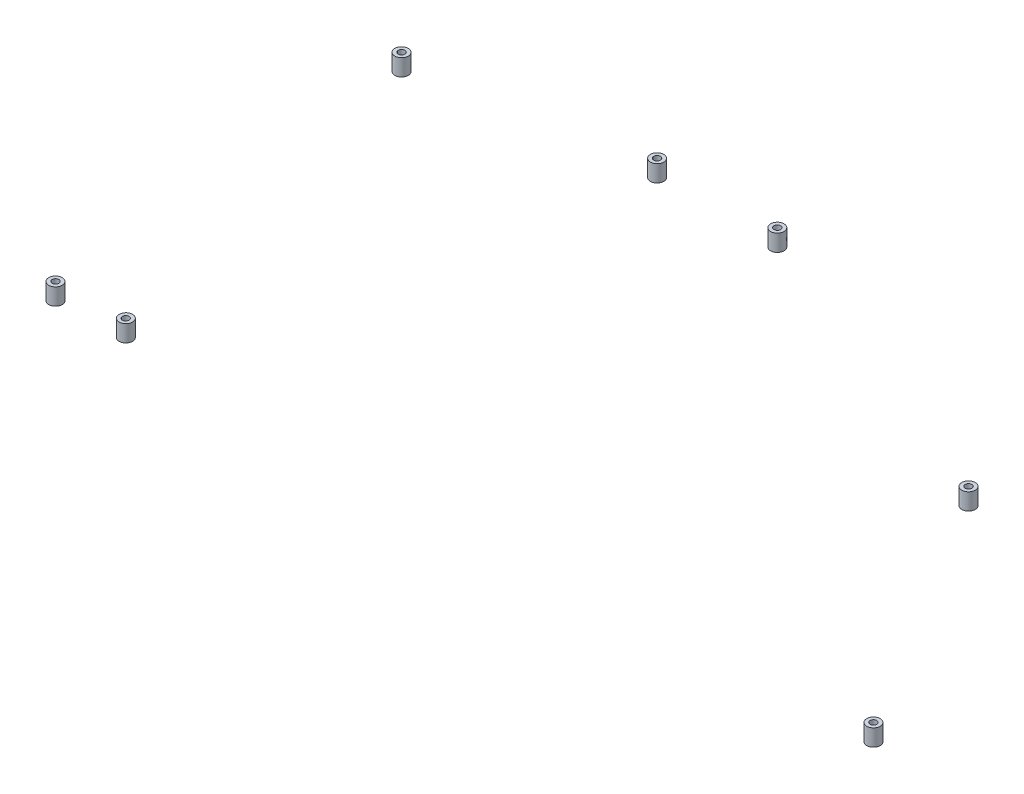
SolidWorks part; units mm, degrees
material "PP Kopolimer"
ref_plane "Płaszczyzna XY" through (0, 0, 0) normal (0, 0, 1) x (1, 0, 0)
ref_plane "Płaszczyzna XZ" through (0, 0, 0) normal (0, 1, 0) x (1, 0, 0)
ref_plane "Płaszczyzna YZ" through (0, 0, 0) normal (1, 0, 0) x (0, 0, -1)
sketch "Szkic1" plane through (0, 455.3, 0) normal (0, 1, 0) x (1, 0, 0)
  circle A0 centre (-557.5005, -428.0764) radius 4 construction
  circle A1 centre (-517.5005, -426.0794) radius 4 construction
  circle A2 centre (-85.5135, -411.9205) radius 4 construction
  circle A4 centre (-179.1662, -261.5446) radius 4 construction
  circle A6 centre (-369.9079, -184.9064) radius 4 construction
  circle A7 centre (-441.6637, -184.9064) radius 4 construction
  circle A8 centre (-572.688, -206.3657) radius 4 construction
  circle A9 centre (-557.5005, -428.0764) radius 4
  circle A10 centre (-517.5005, -426.0794) radius 4
  circle A11 centre (-85.5135, -411.9205) radius 4
  circle A13 centre (-179.1662, -261.5446) radius 4
  circle A15 centre (-369.9079, -184.9064) radius 4
  circle A16 centre (-441.6637, -184.9064) radius 4
  circle A17 centre (-572.688, -206.3657) radius 4
  circle A18 centre (-557.5005, -428.0452) radius 2 construction
  circle A19 centre (-517.5005, -426.1747) radius 2 construction
  circle A20 centre (-85.5135, -411.9205) radius 2 construction
  circle A22 centre (-179.1662, -261.5446) radius 2 construction
  circle A24 centre (-369.9079, -184.9064) radius 2 construction
  circle A25 centre (-441.6637, -184.9064) radius 2 construction
  circle A26 centre (-572.688, -206.3657) radius 2 construction
  circle A27 centre (-557.5005, -428.0452) radius 2
  circle A28 centre (-517.5005, -426.1747) radius 2
  circle A29 centre (-85.5135, -411.9205) radius 2
  circle A31 centre (-179.1662, -261.5446) radius 2
  circle A33 centre (-369.9079, -184.9064) radius 2
  circle A34 centre (-441.6637, -184.9064) radius 2
  circle A35 centre (-572.688, -206.3657) radius 2
extrude "Dodanie-wyciągnięcie1" add sketch "Szkic1" against normal blind 10
